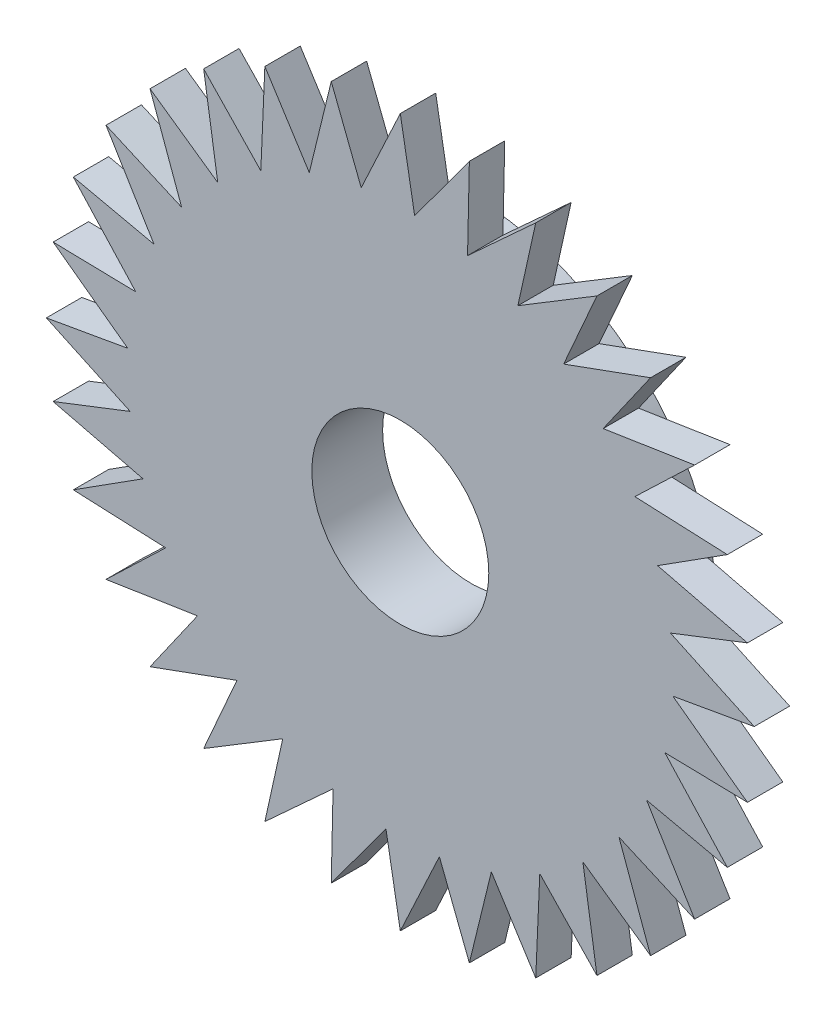
SolidWorks part; units mm, degrees
ref_plane "Ön Düzlem" through (0, 0, 0) normal (0, 0, 1) x (1, 0, 0)
ref_plane "Üst Düzlem" through (0, 0, 0) normal (0, 1, 0) x (1, 0, 0)
ref_plane "Sağ Düzlem" through (0, 0, 0) normal (1, 0, 0) x (0, 0, -1)
sketch "Çizim1" plane through (0, 0, 0) normal (0, 0, 1) x (1, 0, 0)
  line L42 (0, 0) -> (0, 6.3915)
  line L43 (0, 10) -> (0.4055, 7.7002)
  line L44 (0, 10) -> (-1.1045, 7.6314)
  line L45 (1.9509, 9.8079) -> (0.4055, 7.7002)
  line L46 (1.9509, 9.8079) -> (1.9, 7.4731)
  line L47 (3.8268, 9.2388) -> (1.9, 7.4731)
  line L48 (3.8268, 9.2388) -> (3.3214, 6.9589)
  line L49 (5.5557, 8.3147) -> (3.3214, 6.9589)
  line L50 (5.5557, 8.3147) -> (4.6152, 6.1772)
  line L51 (7.0711, 7.0711) -> (4.6152, 6.1772)
  line L52 (7.0711, 7.0711) -> (5.7316, 5.1581)
  line L53 (8.3147, 5.5557) -> (5.7316, 5.1581)
  line L54 (8.3147, 5.5557) -> (6.6278, 3.9408)
  line L55 (9.2388, 3.8268) -> (6.6278, 3.9408)
  line L56 (9.2388, 3.8268) -> (7.2692, 2.5721)
  line L57 (9.8079, 1.9509) -> (7.2692, 2.5721)
  line L58 (9.8079, 1.9509) -> (7.6314, 1.1045)
  line L59 (10, 0) -> (7.6314, 1.1045)
  line L60 (10, 0) -> (7.7002, -0.4055)
  line L61 (9.8079, -1.9509) -> (7.7002, -0.4055)
  line L62 (9.8079, -1.9509) -> (7.4731, -1.9)
  line L63 (9.2388, -3.8268) -> (7.4731, -1.9)
  line L64 (9.2388, -3.8268) -> (6.9589, -3.3214)
  line L65 (8.3147, -5.5557) -> (6.9589, -3.3214)
  line L66 (8.3147, -5.5557) -> (6.1772, -4.6152)
  line L67 (7.0711, -7.0711) -> (6.1772, -4.6152)
  line L68 (7.0711, -7.0711) -> (5.1581, -5.7316)
  line L69 (5.5557, -8.3147) -> (5.1581, -5.7316)
  line L70 (5.5557, -8.3147) -> (3.9408, -6.6278)
  line L71 (3.8268, -9.2388) -> (3.9408, -6.6278)
  line L72 (3.8268, -9.2388) -> (2.5721, -7.2692)
  line L73 (1.9509, -9.8079) -> (2.5721, -7.2692)
  line L74 (1.9509, -9.8079) -> (1.1045, -7.6314)
  line L75 (0, -10) -> (1.1045, -7.6314)
  line L76 (0, -10) -> (-0.4055, -7.7002)
  line L77 (-1.9509, -9.8079) -> (-0.4055, -7.7002)
  line L78 (-1.9509, -9.8079) -> (-1.9, -7.4731)
  line L79 (-3.8268, -9.2388) -> (-1.9, -7.4731)
  line L80 (-3.8268, -9.2388) -> (-3.3214, -6.9589)
  line L81 (-5.5557, -8.3147) -> (-3.3214, -6.9589)
  line L82 (-5.5557, -8.3147) -> (-4.6152, -6.1772)
  line L83 (-7.0711, -7.0711) -> (-4.6152, -6.1772)
  line L84 (-7.0711, -7.0711) -> (-5.7316, -5.1581)
  line L85 (-8.3147, -5.5557) -> (-5.7316, -5.1581)
  line L86 (-8.3147, -5.5557) -> (-6.6278, -3.9408)
  line L87 (-9.2388, -3.8268) -> (-6.6278, -3.9408)
  line L88 (-9.2388, -3.8268) -> (-7.2692, -2.5721)
  line L89 (-9.8079, -1.9509) -> (-7.2692, -2.5721)
  line L90 (-9.8079, -1.9509) -> (-7.6314, -1.1045)
  line L91 (-10, 0) -> (-7.6314, -1.1045)
  line L92 (-10, 0) -> (-7.7002, 0.4055)
  line L93 (-9.8079, 1.9509) -> (-7.7002, 0.4055)
  line L94 (-9.8079, 1.9509) -> (-7.4731, 1.9)
  line L95 (-9.2388, 3.8268) -> (-7.4731, 1.9)
  line L96 (-9.2388, 3.8268) -> (-6.9589, 3.3214)
  line L97 (-8.3147, 5.5557) -> (-6.9589, 3.3214)
  line L98 (-8.3147, 5.5557) -> (-6.1772, 4.6152)
  line L99 (-7.0711, 7.0711) -> (-6.1772, 4.6152)
  line L100 (-7.0711, 7.0711) -> (-5.1581, 5.7316)
  line L101 (-5.5557, 8.3147) -> (-5.1581, 5.7316)
  line L102 (-5.5557, 8.3147) -> (-3.9408, 6.6278)
  line L103 (-3.8268, 9.2388) -> (-3.9408, 6.6278)
  line L104 (-3.8268, 9.2388) -> (-2.5721, 7.2692)
  line L105 (-1.9509, 9.8079) -> (-2.5721, 7.2692)
  line L106 (-1.9509, 9.8079) -> (-1.1045, 7.6314)
  point P38 (0, 0)
  point P125 (0, 0)
  dimension "D3" = 10
  dimension "D4" = 25
  dimension "D5" = 32
extrude "Yükseklik-Ekstrüzyon1" add sketch "Çizim1" along normal blind 1 contours L106 L105 L104 L103 L102 L101 L100 L99 L98 L97 L96 L95 L94 L93 L92 L91 L90 L89 L88 L87 L86 L85 L84 L83 L82 L81 L80 L79 L78 L77 L76 L75 L74 L73 L72 L71 L70 L69 L68 L67 L66 L65 L64 L63 L62 L61 L60 L59 L58 L57 L56
sketch "Çizim3" plane through (0, 0, 0) normal (0, 0, -1) x (-1, 0, 0)
  circle A0 centre (0, 0) radius 7
  dimension "D1" = 14
extrude "Yükseklik-Ekstrüzyon2" add sketch "Çizim3" along normal blind 1
sketch "Çizim4" plane through (0, 0, -1) normal (0, 0, -1) x (-1, 0, 0)
  circle A0 centre (0, 0) radius 2.5
  dimension "D1" = 5
extrude "Kes-Ekstrüzyon1" cut sketch "Çizim4" against normal blind 4
